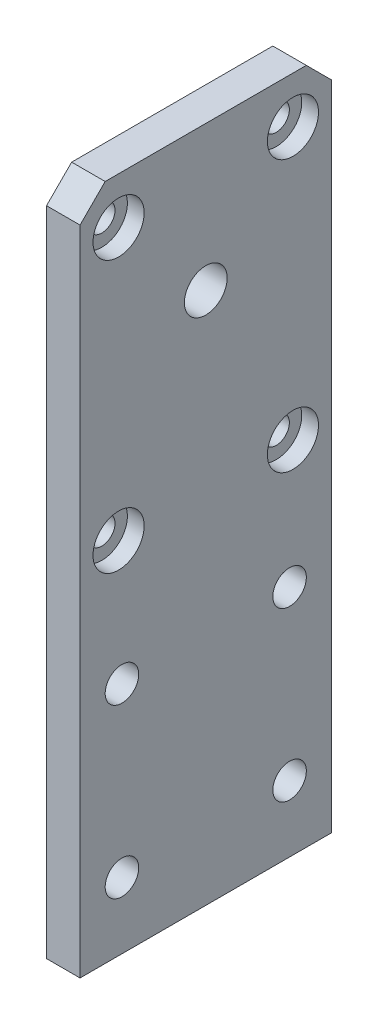
SolidWorks part; units mm, degrees
ref_plane "Alzado" through (0, 0, 0) normal (0, 0, 1) x (1, 0, 0)
ref_plane "Planta" through (0, 0, 0) normal (0, 1, 0) x (1, 0, 0)
ref_plane "Vista lateral" through (0, 0, 0) normal (1, 0, 0) x (0, 0, -1)
sketch "Croquis1" plane through (0, 0, 0) normal (1, 0, 0) x (0, 0, -1)
  line L1 (-15, -40.4) -> (15, -40.4)
  line L2 (-15, -40.4) -> (-15, 40.4)
  line L3 (-15, 40.4) -> (15, 40.4)
  line L4 (15, -40.4) -> (15, 40.4)
  line L5 (-15, -40.4) -> (15, 40.4) construction
  line L6 (-15, 40.4) -> (15, -40.4) construction
  point P0 (0, 0)
  dimension "D1" = 30
  dimension "D2" = 80.8
extrude "Saliente-Extruir1" add sketch "Croquis1" along normal blind 4
sketch "Croquis3" plane through (4, 0, 0) normal (1, 0, 0) x (0, 0, -1)
  line L0 (-10, -12.5) -> (10, -12.5) construction
  line L1 (0, -12.5) -> (0, -40.4) construction
  line L2 (-15, -40.4) -> (15, -40.4) construction
  line L3 (15, 40.4) -> (-15, 40.4) construction
  circle A0 centre (-10, -12.5) radius 2
  circle A1 centre (10, -12.5) radius 2
  circle A2 centre (0, -12.5) radius 2 construction
  circle A3 centre (-10, -32.5) radius 2
  circle A4 centre (0, -32.5) radius 2 construction
  circle A5 centre (10, -32.5) radius 2
  dimension "D2" = 4
  dimension "D1" = 52.9
  dimension "D3" = 20
  dimension "D5" = 20
  dimension "D4" = 2
extrude "Cortar-Extruir2" cut sketch "Croquis3" against normal through all
sketch "Croquis8" plane through (0, 0, 0) normal (-1, 0, 0) x (0, 0, 1)
  circle A0 centre (0, 23.15) radius 2.55
  circle A1 centre (10, -12.5) radius 2 construction
  dimension "D2" = 5.1
  dimension "D1" = 35.65
extrude "Cortar-Extruir3" cut sketch "Croquis8" against normal through all
sketch "Croquis10" plane through (4, 0, 0) normal (-1, 0, 0) x (0, 0, 1)
  line L0 (-15, 40.4) -> (15, 40.4) construction
  line L1 (-10.4, 34.85) -> (10.4, 34.85) construction
  line L2 (0, 34.85) -> (0, 40.4) construction
  circle A0 centre (-10.4, 34.85) radius 3.05
  circle A1 centre (10.4, 34.85) radius 3.05
  circle A2 centre (10.4, 2.5) radius 3.05
  circle A3 centre (-10.4, 2.5) radius 3.05
  circle A4 centre (-10, -12.5) radius 2 construction
  dimension "D1" = 6.1
  dimension "D2" = 32.35
  dimension "D3" = 20.8
  dimension "D5" = 15
extrude "Cortar-Extruir4" cut sketch "Croquis10" along normal blind 2
sketch "Croquis11" plane through (2, 0, 0) normal (1, 0, 0) x (0, 0, -1)
  circle A0 centre (-10.4, 34.85) radius 1.575
  circle A1 centre (10.4, 34.85) radius 1.575
  circle A2 centre (10.4, 2.5) radius 1.575
  circle A3 centre (-10.4, 2.5) radius 1.575
  dimension "D1" = 3.15
extrude "Cortar-Extruir5" cut sketch "Croquis11" against normal through all
chamfer "Chaflán1" distance 3 angle 45 2 edges at (2, 40.4, -15) (2, 40.4, 15)
